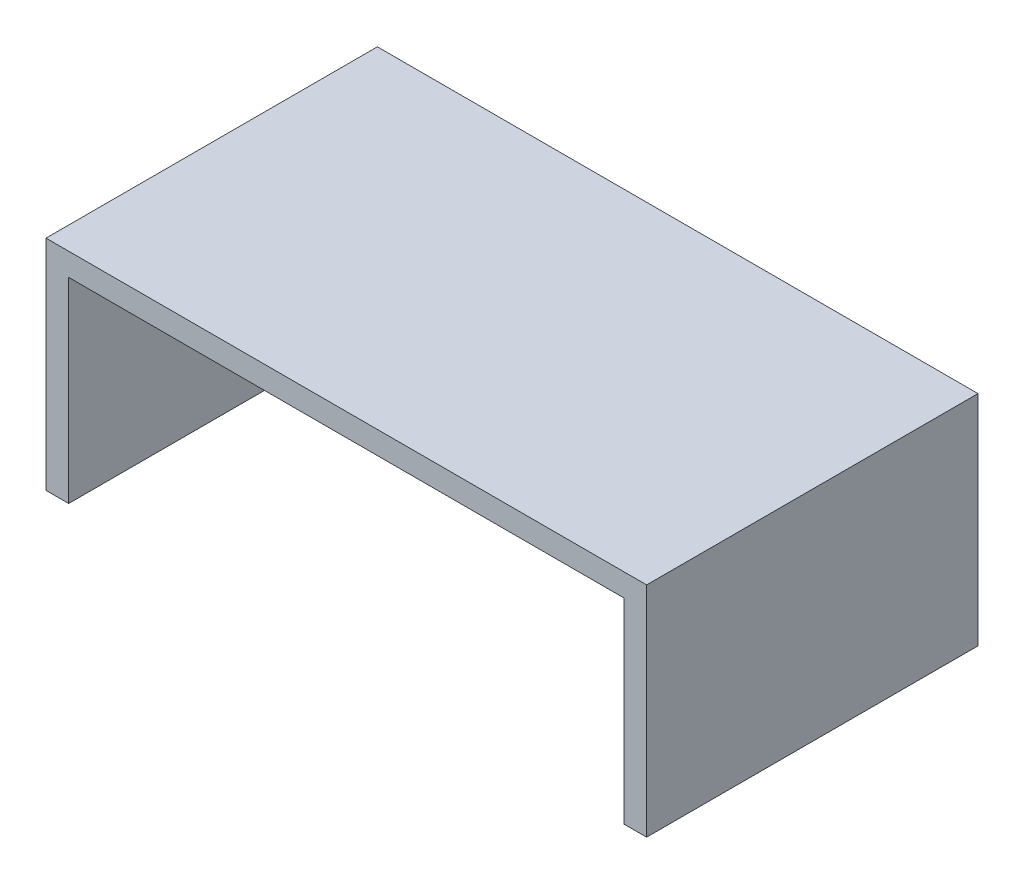
SolidWorks part; units mm, degrees
ref_plane "前基準面" through (0, 0, 0) normal (0, 0, 1) x (1, 0, 0)
ref_plane "上基準面" through (0, 0, 0) normal (0, 1, 0) x (1, 0, 0)
ref_plane "右基準面" through (0, 0, 0) normal (1, 0, 0) x (0, 0, -1)
sketch "草圖1" plane through (0, 0, 0) normal (0, 1, 0) x (1, 0, 0)
  line L1 (-66.25, 36.55) -> (66.25, 36.55)
  line L2 (-66.25, 36.55) -> (-66.25, -36.55)
  line L3 (-66.25, -36.55) -> (66.25, -36.55)
  line L4 (66.25, 36.55) -> (66.25, -36.55)
  line L5 (0, -36.55) -> (0, 36.55) construction
  line L6 (-66.25, 0) -> (66.25, 0) construction
  point P1 (0, 0)
  dimension "D1" = 132.5
  dimension "D2" = 73.1
extrude "填料-伸長1" add sketch "草圖1" along normal blind 48.2 contours L1 L4 L3 L2
sketch "草圖3" plane through (0, 0, 36.55) normal (0, 0, 1) x (1, 0, 0)
  line L0 (-66.25, 0) -> (66.25, 0) construction
  line L1 (-61.25, 0) -> (61.25, 0)
  line L2 (-61.25, 0) -> (-61.25, 43.2)
  line L3 (-61.25, 43.2) -> (61.25, 43.2)
  line L4 (61.25, 0) -> (61.25, 43.2)
  line L5 (-66.25, 48.2) -> (-66.25, 0) construction
  dimension "D1" = 122.5
  dimension "D2" = 5
  dimension "D3" = 43.2
extrude "除料-伸長1" cut sketch "草圖3" against normal blind 68.1
sketch "草圖6" plane through (-66.25, 0, 0) normal (-1, 0, 0) x (0, 0, 1)
  line L0 (-36.55, 48.2) -> (36.55, 48.2) construction
  line L1 (-10, 43.2) -> (10, 43.2)
  line L2 (-10, 43.2) -> (-10, 33.2)
  line L3 (-10, 33.2) -> (10, 33.2)
  line L4 (10, 43.2) -> (10, 33.2)
  line L5 (0, 33.2) -> (0, 43.2) construction
  line L6 (-10, 38.2) -> (10, 38.2) construction
  point P0 (0, 38.2)
  dimension "D1" = 20
  dimension "D2" = 10
  dimension "D3" = 5
extrude "除料-伸長2" cut sketch "草圖6" against normal blind 5
sketch "草圖7" plane through (-66.25, 0, 0) normal (-1, 0, 0) x (0, 0, 1)
  line L1 (-128.8989, 44.3232) -> (-92.8917, 44.3232)
  line L2 (-128.8989, 44.3232) -> (-128.8989, 58.7301)
  line L3 (-128.8989, 58.7301) -> (-92.8917, 58.7301)
  line L4 (-92.8917, 44.3232) -> (-92.8917, 58.7301)
